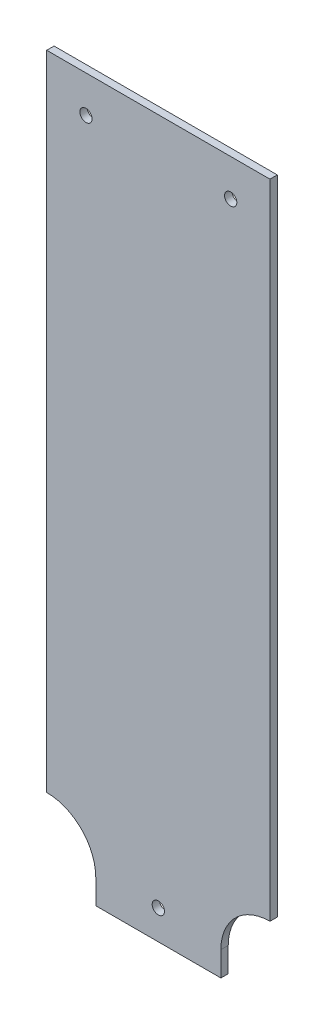
SolidWorks part; units mm, degrees
ref_plane "Face" through (0, 0, 0) normal (0, 0, 1) x (1, 0, 0)
ref_plane "Dessus" through (0, 0, 0) normal (0, 1, 0) x (1, 0, 0)
ref_plane "Droite" through (0, 0, 0) normal (1, 0, 0) x (0, 0, -1)
sketch "Esquisse1" plane through (0, 0, 0) normal (0, 0, 1) x (1, 0, 0)
  line L0 (0, 0) -> (0, 292) construction
  line L1 (45.5, 292) -> (-45.5, 292)
  line L2 (-45.5, 292) -> (-45.5, 30)
  line L3 (25.5, 0) -> (-25.5, 0)
  line L4 (-25.5, 0) -> (-25.5, 10)
  line L5 (-45.5, 30) -> (-45.5, 60) construction
  line L6 (45.5, 30) -> (45.5, 60) construction
  line L7 (25.5, 0) -> (25.5, 10)
  line L8 (45.5, 292) -> (45.5, 30)
  arc A0 (-45.5, 30) -> (-25.5, 10) centre (-45.5, 10) cw
  arc A1 (45.5, 30) -> (25.5, 10) centre (45.5, 10) ccw
  circle A2 centre (-29.5, 277) radius 2.5
  circle A3 centre (29.5, 277) radius 2.5
  circle A4 centre (0, 12) radius 2.5
  dimension "D3" = 20
  dimension "D5" = 16
  dimension "D7" = 5
  dimension "D8" = 12
  dimension "D1" = 292
  dimension "D2" = 45.5
  dimension "D4" = 30
  dimension "D6" = 15
extrude "Extrusion1" add sketch "Esquisse1" along normal blind 3
